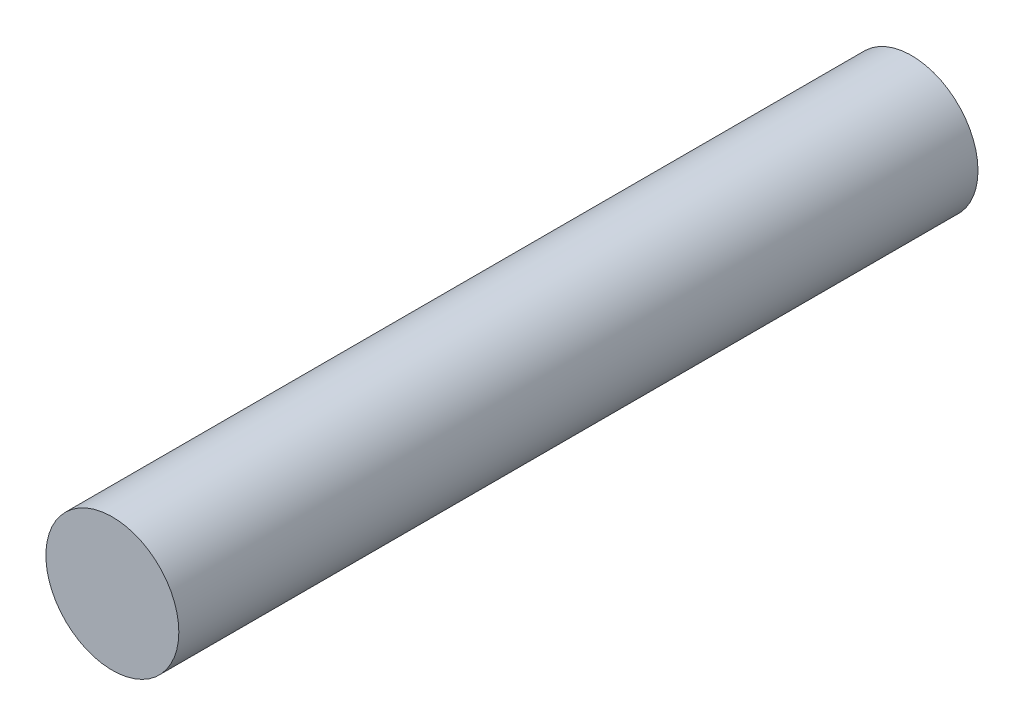
SolidWorks part; units mm, degrees
ref_plane "Front Plane" through (0, 0, 0) normal (0, 0, 1) x (1, 0, 0)
ref_plane "Top Plane" through (0, 0, 0) normal (0, 1, 0) x (1, 0, 0)
ref_plane "Right Plane" through (0, 0, 0) normal (1, 0, 0) x (0, 0, -1)
sketch "Sketch1" plane through (0, 0, 0) normal (0, 0, 1) x (1, 0, 0)
  circle A0 centre (0, 0) radius 12.4765
  dimension "D1" = 24.953
extrude "Boss-Extrude1" add sketch "Sketch1" along normal blind 150
